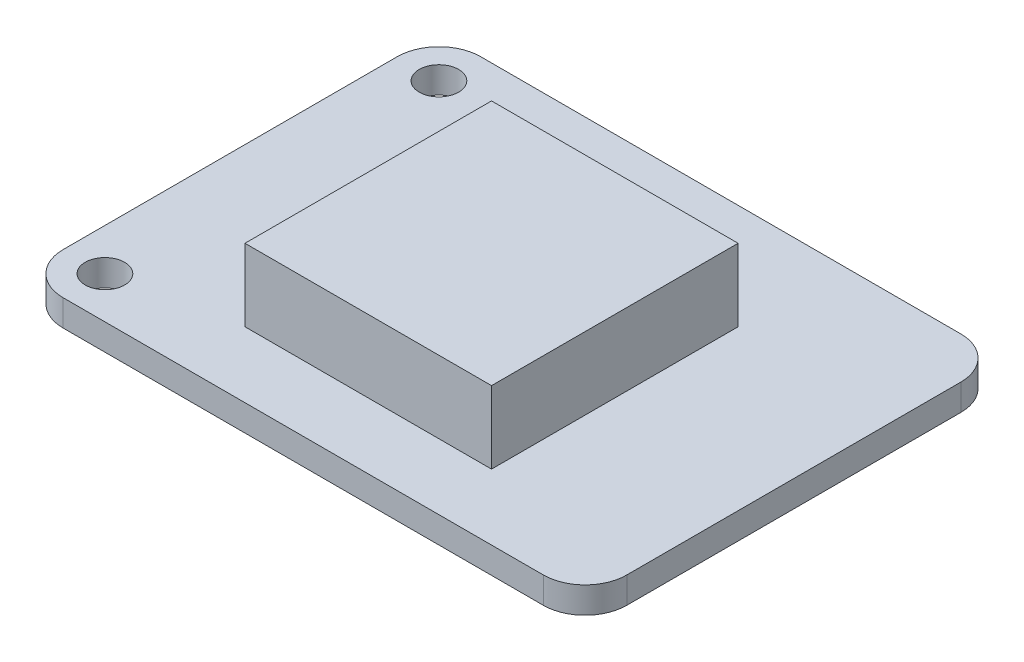
SolidWorks part; units mm, degrees
ref_plane "Front Plane" through (0, 0, 0) normal (0, 0, 1) x (1, 0, 0)
ref_plane "Top Plane" through (0, 0, 0) normal (0, 1, 0) x (1, 0, 0)
ref_plane "Right Plane" through (0, 0, 0) normal (1, 0, 0) x (0, 0, -1)
sketch "Sketch1" plane through (0, 0, 0) normal (0, 1, 0) x (1, 0, 0)
  line L1 (-14.605, -12.7) -> (14.605, -12.7)
  line L2 (-17.145, -10.16) -> (-17.145, 10.16)
  line L3 (-14.605, 12.7) -> (14.605, 12.7)
  line L4 (17.145, -10.16) -> (17.145, 10.16)
  line L5 (-17.145, -12.7) -> (17.145, 12.7) construction
  line L6 (-17.145, 12.7) -> (17.145, -12.7) construction
  arc A0 (14.605, -12.7) -> (17.145, -10.16) centre (14.605, -10.16) ccw
  arc A1 (14.605, 12.7) -> (17.145, 10.16) centre (14.605, 10.16) cw
  arc A2 (-17.145, 10.16) -> (-14.605, 12.7) centre (-14.605, 10.16) cw
  arc A3 (-14.605, -12.7) -> (-17.145, -10.16) centre (-14.605, -10.16) cw
  point P0 (0, 0)
  dimension "D3" = 2.54
  dimension "D1" = 25.4
  dimension "D2" = 34.29
extrude "PCB" add sketch "Sketch1" along normal blind 1.6
hole_wizard "M2 Clearance Hole1" positions "Sketch2" profile "Sketch3" hole size "M2" standard "ANSI Metric" end condition through all
sketch "Sketch2" plane through (0, 1.6, 0) normal (0, 1, 0) x (1, 0, 0)
  line L0 (-14.605, -10.16) -> (-14.605, 10.16) construction
  line L2 (-17.145, 10.16) -> (-17.145, -10.16) construction
  line L3 (-14.605, -12.7) -> (14.605, -12.7) construction
  line L4 (14.605, 12.7) -> (-14.605, 12.7) construction
  point P1 (-14.605, -10.16)
  point P2 (-14.605, 10.16)
  dimension "D1" = 2.54
  dimension "D2" = 2.54
  dimension "D3" = 2.54
sketch "Sketch3" plane through (-14.605, 1.6, 10.16) normal (1, 0, 0) x (0, 0, 1)
  line L0 (0, 0) -> (0, 1.6)
  line L1 (0, 1.6) -> (1.2, 1.6)
  line L2 (1.2, 1.6) -> (1.2, 0)
  line L5 (1.2, 0) -> (0, 0)
  line L11 (0, -6.35) -> (0, 107.95) construction
  dimension "Thru Hole Dia." = 2.4
  dimension "Thru Hole Depth" = 1.6
sketch "Sketch4" plane through (0, 1.6, 0) normal (0, 1, 0) x (1, 0, 0)
  line L0 (-14.605, -12.7) -> (14.605, -12.7) construction
  line L1 (-7.545, -8.7) -> (7.455, -8.7)
  line L2 (-7.545, -8.7) -> (-7.545, 6.3)
  line L3 (-7.545, 6.3) -> (7.455, 6.3)
  line L4 (7.455, -8.7) -> (7.455, 6.3)
  line L5 (-17.145, 10.16) -> (-17.145, -10.16) construction
  dimension "D1" = 15
  dimension "D2" = 15
  dimension "D3" = 4
  dimension "D4" = 9.6
extrude "Antenna" add sketch "Sketch4" along normal blind 4.4
sketch "Sketch5" plane through (0, 0, 0) normal (0, -1, 0) x (1, 0, 0)
  line L0 (-17.145, -10.16) -> (-17.145, 10.16) construction
  circle A0 centre (-9.645, 0) radius 6.5
  dimension "D1" = 13
  dimension "D2" = 7.5
extrude "Battery Holder" add sketch "Sketch5" along normal blind 3.5
